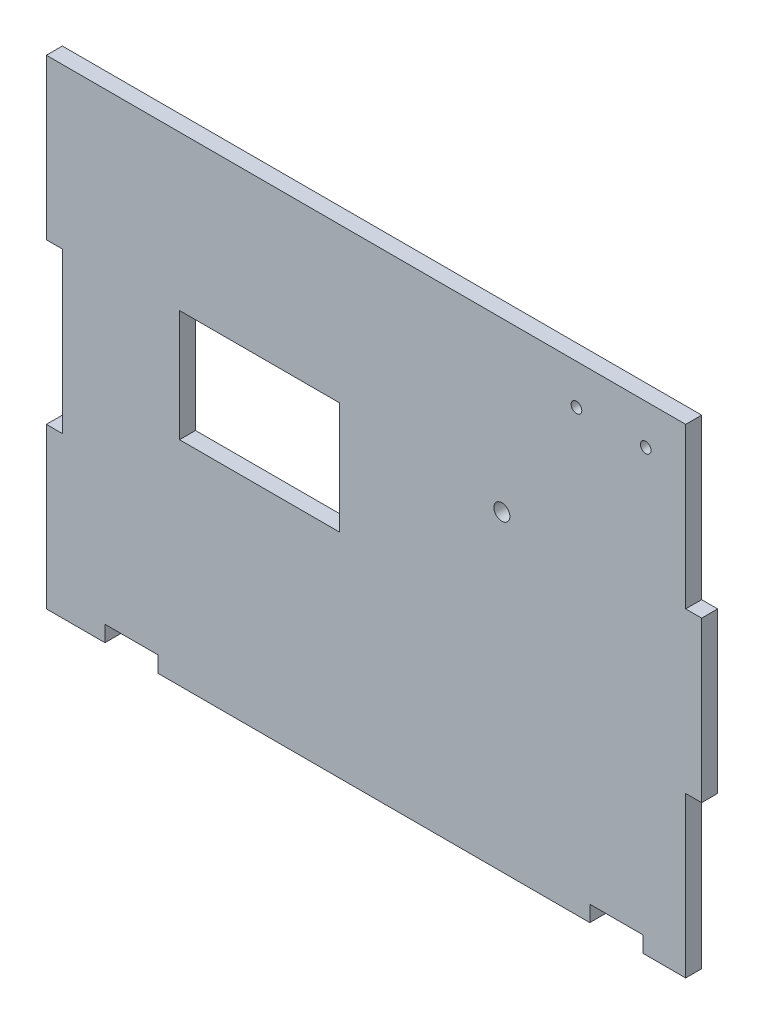
SolidWorks part; units mm, degrees
ref_plane "Front Plane" through (0, 0, 0) normal (0, 0, 1) x (1, 0, 0)
ref_plane "Top Plane" through (0, 0, 0) normal (0, 1, 0) x (1, 0, 0)
ref_plane "Right Plane" through (0, 0, 0) normal (1, 0, 0) x (0, 0, -1)
sketch "Model" plane through (0, 0, 0) normal (0, 0, 1) x (1, 0, 0)
  line L5 (71.2073, 100.9131) -> (71.2073, 70.9131)
  line L6 (-26.7927, 101.9131) -> (3.2073, 101.9131)
  line L7 (3.2073, 101.9131) -> (3.2073, 80.9131)
  line L8 (3.2073, 80.9131) -> (-26.7927, 80.9131)
  line L9 (-26.7927, 80.9131) -> (-26.7927, 101.9131)
  line L10 (-51.7927, 100.9131) -> (-48.7927, 100.9131)
  line L11 (-48.7927, 100.9131) -> (-48.7927, 70.9131)
  line L12 (-48.7927, 70.9131) -> (-51.7927, 70.9131)
  line L20 (44.2573, 40.9131) -> (68.2073, 40.9131) construction
  line L21 (-51.7927, 100.9131) -> (-51.7927, 130.9131)
  line L22 (-51.7927, 70.9131) -> (-51.7927, 40.9131)
  line L37 (-51.7927, 40.9131) -> (44.2573, 40.9131) construction
  line L40 (68.2073, 40.9131) -> (68.2073, 70.9131)
  line L41 (68.2073, 70.9131) -> (71.2073, 70.9131)
  line L59 (71.2073, 100.9131) -> (68.2073, 100.9131)
  line L60 (68.2073, 100.9131) -> (68.2073, 130.9131)
  line L65 (68.2073, 130.9131) -> (-51.7927, 130.9131)
  line L66 (-51.7927, 40.9131) -> (-40.7927, 40.9131)
  line L67 (-40.7927, 40.9131) -> (-40.7927, 43.9131)
  line L68 (-40.7927, 43.9131) -> (-30.7927, 43.9131)
  line L69 (-30.7927, 43.9131) -> (-30.7927, 40.9131)
  line L70 (-30.7927, 40.9131) -> (50.2073, 40.9131)
  line L71 (50.2073, 40.9131) -> (50.2073, 43.9131)
  line L72 (50.2073, 43.9131) -> (60.2073, 43.9131)
  line L73 (60.2073, 43.9131) -> (60.2073, 40.9131)
  line L74 (60.2073, 40.9131) -> (68.2073, 40.9131)
  circle A0 centre (47.7073, 123.4131) radius 1
  circle A1 centre (60.7073, 123.4131) radius 1
  circle A2 centre (33.7073, 99.4131) radius 1.5
  dimension "D4" = 30
  dimension "D5" = 10
  dimension "D6" = 11
  dimension "D11" = 13
  dimension "D14" = 14
  dimension "D17" = 24
  dimension "D3" = 8
  dimension "D7" = 10
  dimension "D8" = 3
  dimension "D9" = 3
  dimension "D10" = 3
  dimension "D12" = 7.5
  dimension "D13" = 7.5
  dimension "D15" = 30
  dimension "D16" = 3
  dimension "D18" = 30
  dimension "D20" = 30
  dimension "D21" = 65
  dimension "3" = 3
  dimension "D23" = 30
  dimension "D24" = 30
  dimension "D25" = 117
extrude "Boss-Extrude1" add sketch "Model" along normal blind 3
